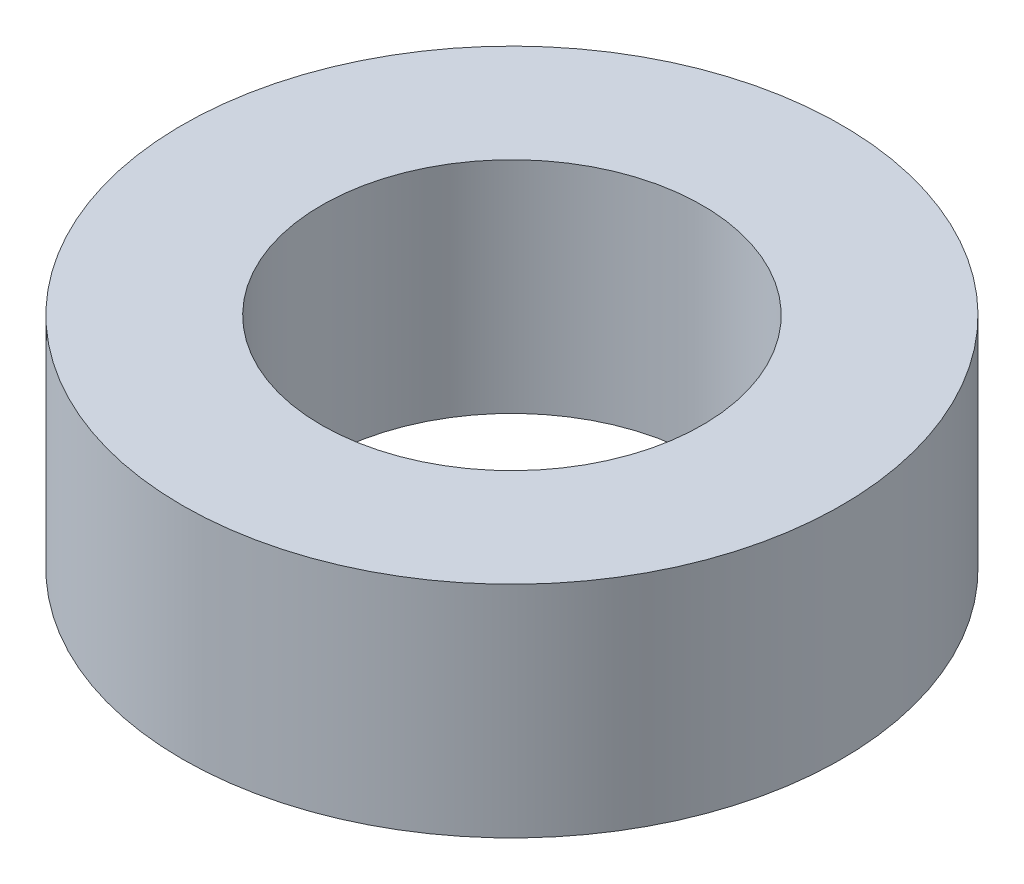
SolidWorks part; units mm, degrees
ref_plane "前视基准面" through (0, 0, 0) normal (0, 0, 1) x (1, 0, 0)
ref_plane "上视基准面" through (0, 0, 0) normal (0, 1, 0) x (1, 0, 0)
ref_plane "右视基准面" through (0, 0, 0) normal (1, 0, 0) x (0, 0, -1)
sketch "草图1" plane through (0, 0, 0) normal (0, 1, 0) x (1, 0, 0)
  circle A0 centre (0, 0) radius 22.5
  circle A1 centre (0, 0) radius 13
  dimension "D1" = 26
  dimension "D2" = 45
extrude "凸台-拉伸1" add sketch "草图1" along normal blind 15
